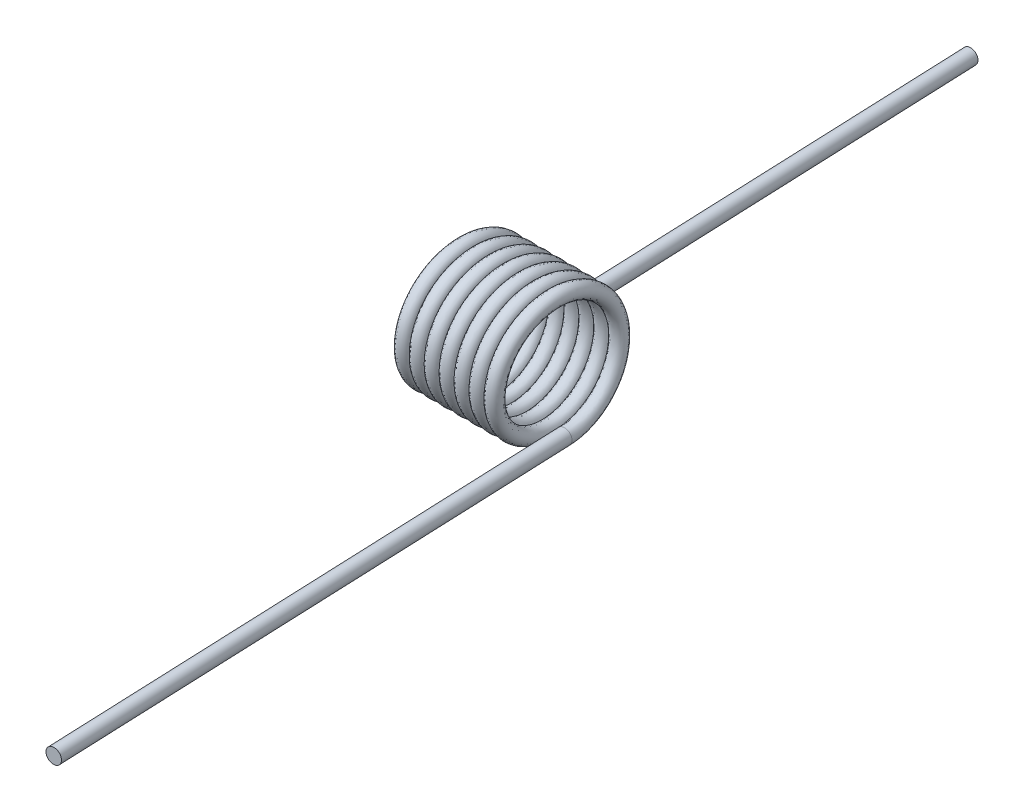
SolidWorks part; units mm, degrees
ref_plane "Front" through (0, 0, 0) normal (0, 0, 1) x (1, 0, 0)
ref_plane "Top" through (0, 0, 0) normal (0, 1, 0) x (1, 0, 0)
ref_plane "Right" through (0, 0, 0) normal (1, 0, 0) x (0, 0, -1)
sketch "Sketch1" plane through (0, 0, 0) normal (1, 0, 0) x (0, 0, -1)
  line L0 (0, 0) -> (0, -1.8288) construction
  line L1 (0, -1.8288) -> (0, -2.0955) construction
  line L2 (0, -2.0955) -> (0, -2.3622) construction
  circle A0 centre (0, 0) radius 1.8288 construction
  circle A1 centre (0, 0) radius 2.3622 construction
  circle A2 centre (0, 0) radius 2.0955
  circle A3 centre (0, -2.0955) radius 0.2667 construction
  circle A4 centre (0, 0) radius 1.3843 construction
curve "Helix/Spiral1" pitch 0.5344 height 3.7408 turns 7
ref_plane "Plane1" through (0, -2.0955, 0) normal (0.0406, 0, 0.9992) x (0.9992, 0, -0.0406)
sketch "Sketch2" plane through (0, -2.0955, 0) normal (0.0406, 0, 0.9992) x (0.9992, 0, -0.0406)
  circle A0 centre (0, 0) radius 0.2667
  dimension "D1" = 0.5334
sweep "Sweep1" add profiles "Sketch2" path "Helix/Spiral1"
sketch "Sketch3" plane through (0, 0, 0) normal (-0.0406, 0, -0.9992) x (-0.9992, 0, 0.0406)
  circle A1 centre (0, -2.0955) radius 0.2667
  circle A2 centre (0, -2.0955) radius 0.2667
  dimension "D1" = 0
extrude "Extrude1" add sketch "Sketch3" along normal blind 19.05
sketch "Sketch4" plane through (0.0062, 0, 0.1516) normal (0.0406, 0, 0.9992) x (0.9955, -0.0856, -0.0404)
  circle A1 centre (3.9034, -1.7678) radius 0.2667
  circle A2 centre (3.9034, -1.7678) radius 0.2667
  dimension "D1" = 0
extrude "Extrude2" add sketch "Sketch4" along normal blind 19.05
sketch "Sketch5" plane through (0, 0, 0) normal (1, 0, 0) x (0, 0, -1)
  circle A0 centre (0, 0) radius 1.3843 construction
  circle A1 centre (0, 0) radius 1.3843
equation "\"D4@Helix/Spiral1\"=\"Wire Dia@Sketch1\"+.001"
equation "\"D1@Sketch2\"=\"Wire Dia@Sketch1\""
equation "\"D1@Extrude2\"=\"Leg Length@Extrude1\""
